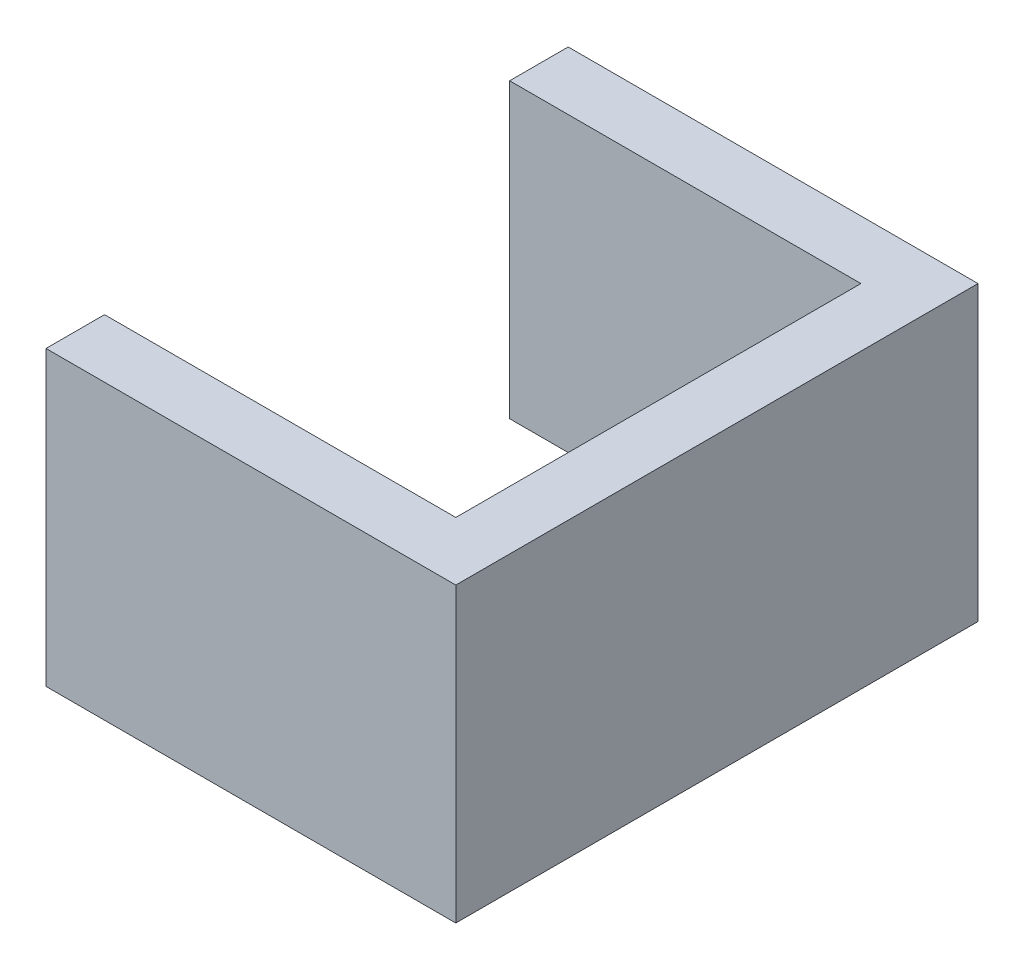
SolidWorks part; units mm, degrees
ref_plane "Front Plane" through (0, 0, 0) normal (0, 0, 1) x (1, 0, 0)
ref_plane "Top Plane" through (0, 0, 0) normal (0, 1, 0) x (1, 0, 0)
ref_plane "Right Plane" through (0, 0, 0) normal (1, 0, 0) x (0, 0, -1)
sketch "Sketch1" plane through (0, 0, 0) normal (0, 1, 0) x (1, 0, 0)
  line L0 (-70.765, 34.8) -> (-10.765, 34.8)
  line L1 (-10.765, 34.8) -> (-10.765, -34.4)
  line L2 (-10.765, -34.4) -> (-70.765, -34.4)
  line L3 (-70.765, -34.4) -> (-70.765, -44.4)
  line L4 (-70.765, -44.4) -> (-0.765, -44.4)
  line L5 (-0.765, -44.4) -> (-0.765, 44.8)
  line L6 (-0.765, 44.8) -> (-70.765, 44.8)
  line L7 (-70.765, 44.8) -> (-70.765, 34.8)
  dimension "D1" = 10
  dimension "D2" = 10
  dimension "D3" = 10
  dimension "D4" = 70
  dimension "D5" = 70
extrude "Boss-Extrude1" add sketch "Sketch1" along normal blind 50
